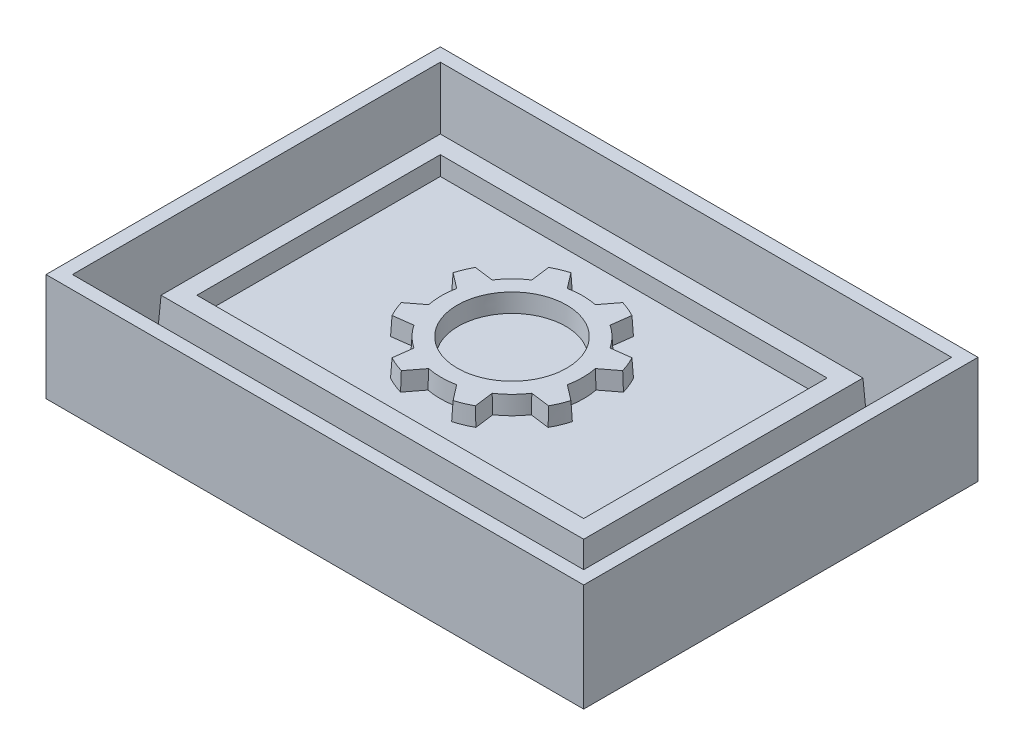
SolidWorks part; units mm, degrees
ref_plane "Front Plane" through (0, 0, 0) normal (0, 0, 1) x (1, 0, 0)
ref_plane "Top Plane" through (0, 0, 0) normal (0, 1, 0) x (1, 0, 0)
ref_plane "Right Plane" through (0, 0, 0) normal (1, 0, 0) x (0, 0, -1)
sketch "Sketch1" plane through (0, 0, 0) normal (0, 1, 0) x (1, 0, 0)
  line L1 (0, 0) -> (76.2, 0)
  line L2 (0, 0) -> (0, 50.8)
  line L3 (0, 50.8) -> (76.2, 50.8)
  line L4 (76.2, 0) -> (76.2, 50.8)
  dimension "D1" = 50.8
  dimension "D2" = 76.2
extrude "Boss-Extrude1" add sketch "Sketch1" along normal blind 12.7 draft 3
sketch "Sketch2" plane through (0, 0, 0) normal (0, -1, 0) x (1, 0, 0)
  line L0 (0, 0) -> (76.2, -50.8) construction
  line L1 (-9.525, 9.525) -> (85.725, 9.525)
  line L2 (-9.525, 9.525) -> (-9.525, -60.325)
  line L3 (-9.525, -60.325) -> (85.725, -60.325)
  line L4 (85.725, 9.525) -> (85.725, -60.325)
  line L5 (-9.525, -60.325) -> (85.725, 9.525) construction
  point P9 (38.1, -25.4)
  point P10 (38.1, -25.4)
  dimension "D1" = 69.85
  dimension "D2" = 95.25
extrude "Boss-Extrude2" add sketch "Sketch2" along normal blind 3.175
sketch "Sketch3" plane through (0, 0, 0) normal (0, 1, 0) x (1, 0, 0)
  line L0 (-9.525, -9.525) -> (-9.525, 60.325) construction
  line L1 (-9.525, 60.325) -> (85.725, 60.325) construction
  line L2 (85.725, 60.325) -> (85.725, -9.525) construction
  line L3 (85.725, -9.525) -> (-9.525, -9.525) construction
  line L4 (-9.525, -9.525) -> (-9.525, 60.325)
  line L5 (-9.525, 60.325) -> (85.725, 60.325)
  line L6 (85.725, 60.325) -> (85.725, -9.525)
  line L7 (85.725, -9.525) -> (-9.525, -9.525)
  line L8 (-6.35, -6.35) -> (-6.35, 57.15)
  line L9 (-6.35, 57.15) -> (82.55, 57.15)
  line L10 (82.55, 57.15) -> (82.55, -6.35)
  line L11 (82.55, -6.35) -> (-6.35, -6.35)
  dimension "D1" = 3.175
extrude "Boss-Extrude3" add sketch "Sketch3" along normal offset from surface (15.875 mm away) 3.175 up to face at (38.1, 12.7, -25.4) offset beyond the face yes
draft "Draft1" type of draft neutral plane draft angle 3 faces to draft 4 face at (82.55, 7.9375, -25.4) face at (38.1, 7.9375, -57.15) face at (38.1, 7.9375, 6.35) face at (-6.35, 7.9375, -25.4) neutral plane through (0, 0, 0) neutral plane normal (0, 1, 0) parameters "D1"=3
sketch "Sketch4" plane through (0, 12.7, 0) normal (0, 1, 0) x (1, 0, 0)
  line L0 (0.6656, 50.1344) -> (0.6656, 0.6656) construction
  line L1 (3.8406, 46.9594) -> (72.3594, 46.9594)
  line L2 (3.8406, 46.9594) -> (3.8406, 3.8406)
  line L3 (3.8406, 3.8406) -> (72.3594, 3.8406)
  line L4 (72.3594, 46.9594) -> (72.3594, 3.8406)
  line L5 (75.5344, 0.6656) -> (75.5344, 50.1344) construction
  line L6 (0.6656, 0.6656) -> (75.5344, 0.6656) construction
  line L7 (75.5344, 50.1344) -> (0.6656, 50.1344) construction
  dimension "D1" = 3.175
  dimension "D2" = 3.175
  dimension "D3" = 3.175
  dimension "D4" = 3.175
extrude "Cut-Extrude1" cut sketch "Sketch4" against normal blind 3.175 draft 3
sketch "Sketch6" plane through (0, 9.525, 0) normal (0, 1, 0) x (1, 0, 0)
  line L0 (38.1, 38.1) -> (38.1, 12.7) construction
  line L1 (38.1, 25.4) -> (42.9601, 37.1333) construction
  line L2 (38.1, 25.4) -> (33.2399, 37.1333) construction
  line L5 (-9.525, 60.325) -> (85.725, -9.525) construction
  line L7 (38.1, 25.4) -> (47.625, 25.4) construction
  circle A0 centre (38.1, 25.4) radius 9.525
  circle A1 centre (38.1, 25.4) radius 12.7
  dimension "D1" = 25.4
  dimension "D2" = 19.05
  dimension "D5" = 45
  dimension "D6" = 22.5
extrude "Boss-Extrude5" add sketch "Sketch6" along normal up to surface (3.175 mm away) up to face at (38.1, 12.7, -25.4)
sketch "Sketch7" plane through (0, 12.7, 0) normal (0, 1, 0) x (1, 0, 0)
  line L0 (38.1, 25.4) -> (38.1, 38.1) construction
  line L1 (42.6242, 40.6167) -> (40.5152, 37.8682)
  line L2 (38.1, 25.4) -> (42.9601, 37.1333) construction
  line L3 (45.6607, 39.3589) -> (45.2085, 35.9242)
  circle A0 centre (38.1, 25.4) radius 12.7 construction
  circle A1 centre (38.1, 25.4) radius 12.7 construction
  arc A2 (45.2085, 35.9242) -> (40.5152, 37.8682) centre (38.1, 25.4) ccw
  arc A3 (45.6607, 39.3589) -> (42.6242, 40.6167) centre (38.1, 25.4) ccw
  dimension "D2" = 31.75
  dimension "D1" = 22.5
  dimension "D3" = 30
  dimension "D4" = 5.08
extrude "Boss-Extrude6" add sketch "Sketch7" against normal up to next
pattern_circular "CirPattern1" count 8 over 360 about axis through (38.1, 0, -25.4) along (0, 1, 0) of "Boss-Extrude6"
draft "Draft2" type of draft neutral plane draft angle 3 faces to draft 33 face at (30.7654, 11.1125, -37.6415) face at (32.0412, 11.1125, -40.0272) face at (34.6303, 11.1125, -39.2425) face at (50.6841, 11.1125, -25.4) face at (38.1, 12.7, -34.925) face at (46.9983, 11.1125, -34.2983) face at (45.4346, 11.1125, -37.6415) face at (44.1588, 11.1125, -40.0272) face at (41.5697, 11.1125, -39.2425) face at (38.1, 11.1125, -37.9841) face at (51.9425, 11.1125, -28.8697) face at (52.7272, 11.1125, -31.4588) face at (50.3415, 11.1125, -32.7346) face at (46.9983, 11.1125, -16.5017) face at (50.3415, 11.1125, -18.0654) face at (41.5697, 11.1125, -11.5575) face at (52.7272, 11.1125, -19.3412) face at (51.9425, 11.1125, -21.9303) face at (38.1, 11.1125, -12.8159) face at (44.1588, 11.1125, -10.7728) face at (45.4346, 11.1125, -13.1585) face at (29.2017, 11.1125, -16.5017) face at (30.7654, 11.1125, -13.1585) face at (32.0412, 11.1125, -10.7728) face at (34.6303, 11.1125, -11.5575) face at (25.5159, 11.1125, -25.4) face at (24.2575, 11.1125, -21.9303) face at (23.4728, 11.1125, -19.3412) face at (25.8585, 11.1125, -18.0654) face at (29.2017, 11.1125, -34.2983) face at (25.8585, 11.1125, -32.7346) face at (23.4728, 11.1125, -31.4588) face at (24.2575, 11.1125, -28.8697) neutral plane through (0, 9.525, 0) neutral plane normal (0, 1, 0) parameters "D1"=3
